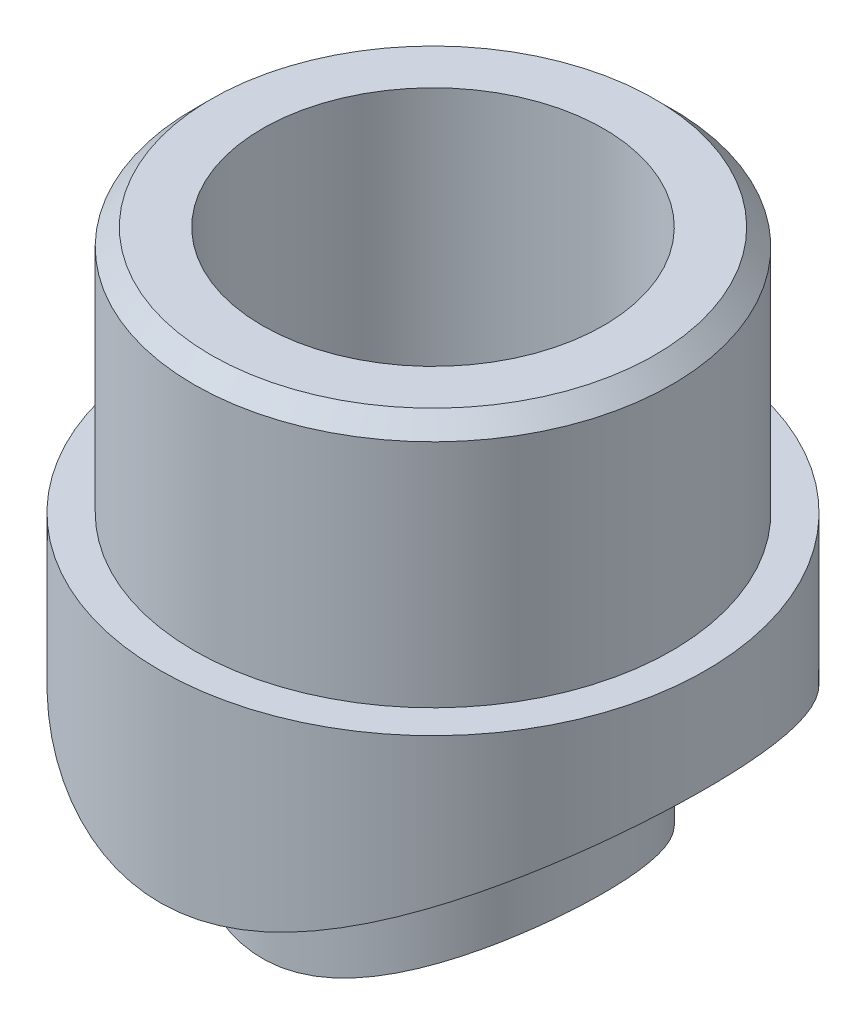
SolidWorks part; units mm, degrees
ref_plane "Front Plane" through (0, 0, 0) normal (0, 0, 1) x (1, 0, 0)
ref_plane "Top Plane" through (0, 0, 0) normal (0, 1, 0) x (1, 0, 0)
ref_plane "Right Plane" through (0, 0, 0) normal (1, 0, 0) x (0, 0, -1)
sketch "Sketch1" plane through (0, 0, 0) normal (0, 1, 0) x (1, 0, 0)
  circle A0 centre (0, 0) radius 16
  circle A1 centre (0, 0) radius 6.6
  dimension "D1" = 32
  dimension "D2" = 13.2
extrude "Boss-Extrude1" add sketch "Sketch1" along normal blind 31
sketch "Sketch2" plane through (0, 31, 0) normal (0, 1, 0) x (1, 0, 0)
  circle A0 centre (0, 0) radius 14
  circle A1 centre (0, 0) radius 10
  dimension "D1" = 28
  dimension "D2" = 20
extrude "Boss-Extrude2" add sketch "Sketch2" along normal blind 14.5
sketch "Sketch3" plane through (0, 0, 0) normal (1, 0, 0) x (0, 0, -1)
  circle A0 centre (0, 0) radius 25
  dimension "D1" = 50
extrude "Cut-Extrude1" cut sketch "Sketch3" against normal through all both and the other way through all
sketch "Sketch4" plane through (0, 0, 0) normal (0, 1, 0) x (1, 0, 0)
  circle A0 centre (0, 0) radius 6.6
  circle A1 centre (0, 0) radius 10
extrude "Boss-Extrude3" add sketch "Sketch4" along normal up to next
sketch "Sketch5" plane through (0, 0, 0) normal (1, 0, 0) x (0, 0, -1)
  circle A0 centre (0, 0) radius 16.7
  dimension "D1" = 33.4
extrude "Cut-Extrude2" cut sketch "Sketch5" against normal through all both and the other way through all
chamfer "Chamfer1" distance 1 angle 45 1 edges at (0, 45.5, 14)
